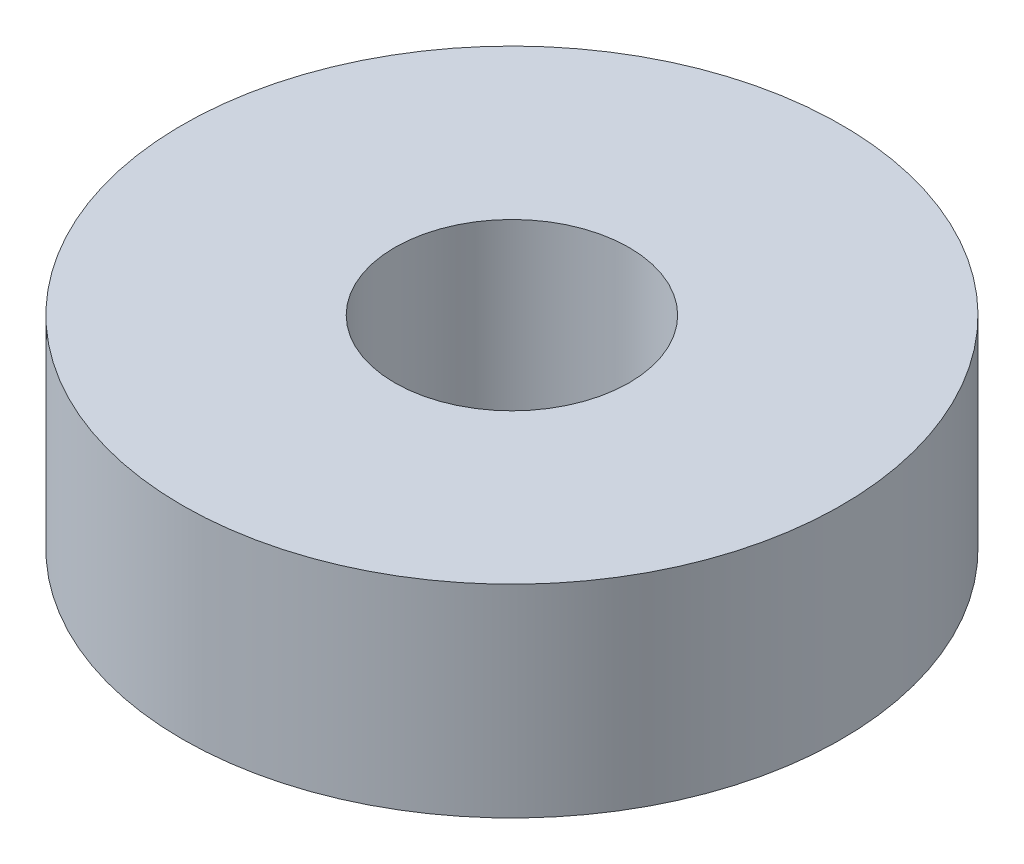
SolidWorks part; units mm, degrees
ref_plane "Front Plane" through (0, 0, 0) normal (0, 0, 1) x (1, 0, 0)
ref_plane "Top Plane" through (0, 0, 0) normal (0, 1, 0) x (1, 0, 0)
ref_plane "Right Plane" through (0, 0, 0) normal (1, 0, 0) x (0, 0, -1)
sketch "Sketch1" plane through (0, 0, 0) normal (0, 1, 0) x (1, 0, 0)
  circle A0 centre (0, 0) radius 10.825
  circle A1 centre (0, 0) radius 3.85
  dimension "D1" = 21.65
  dimension "D2" = 7.7
extrude "Boss-Extrude1" add sketch "Sketch1" along normal blind 6.65
